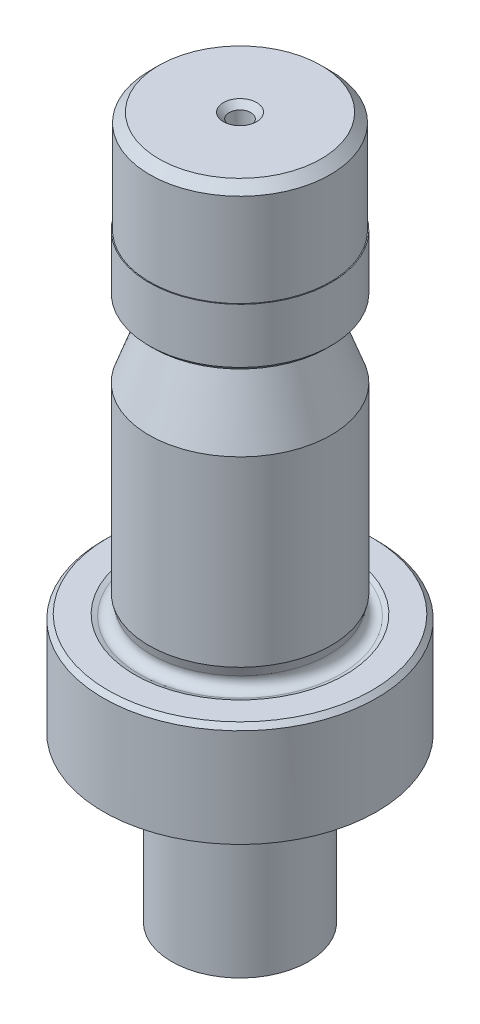
SolidWorks part; units mm, degrees
material "D2 (1.2379)"
ref_plane "Plano frontal" through (0, 0, 0) normal (0, 0, 1) x (1, 0, 0)
ref_plane "Plano superior" through (0, 0, 0) normal (0, 1, 0) x (1, 0, 0)
ref_plane "Plano direito" through (0, 0, 0) normal (1, 0, 0) x (0, 0, -1)
sketch "Esboço1" plane through (0, 0, 0) normal (0, 0, 1) x (1, 0, 0)
  line L0 (0, 77) -> (0, 0) construction
  line L1 (0, 77) -> (8.9, 77)
  line L2 (9.9, 76) -> (9.9, 65.8)
  line L3 (9.9, 65.8) -> (10, 65.8)
  line L4 (10, 65.8) -> (10, 59.8)
  line L5 (9.5, 59.3) -> (8.5164, 59.3)
  line L6 (7.5767, 57.958) -> (10, 51.3)
  line L7 (10, 51.3) -> (10, 31.3)
  line L8 (10, 31.3) -> (9.7321, 30.3)
  line L9 (11.0568, 29.1078) -> (11.5568, 29.3)
  line L10 (11.5568, 29.3) -> (14.5, 29.3)
  line L11 (15, 28.8) -> (15, 0)
  line L12 (15, 0) -> (0, 0)
  line L13 (8.9, 77) -> (9.9, 76)
  line L14 (14.5, 29.3) -> (15, 28.8)
  line L15 (10, 59.8) -> (9.5, 59.3)
  line L16 (0, 77) -> (0, 0)
  arc A0 (8.5164, 59.3) -> (7.5767, 57.958) centre (8.5164, 58.3) ccw
  arc A1 (9.7321, 30.3) -> (11.0568, 29.1078) centre (10.698, 30.0412) ccw
  point P3 (9.9, 77)
  point P6 (10, 59.3)
  point P15 (15, 29.3)
  dimension "D9" = 1
  dimension "D10" = 1
  dimension "D1" = 11.2
  dimension "D2" = 17.7
  dimension "D3" = 25.7
  dimension "D5" = 2
  dimension "D6" = 1
  dimension "D7" = 15
  dimension "D8" = 0.5
  dimension "D11" = 20
  dimension "D12" = 1
  dimension "D14" = 0.5
  dimension "D16" = 0.5
  dimension "D18" = 19.8
  dimension "D19" = 20
  dimension "D20" = 20
  dimension "Backing" = 30
  dimension "D22" = 77
  dimension "D4" = 30
revolve "Revolução1" add sketch "Esboço1" angle 360 about L0
hole_wizard "Furo de diâmetro 3/32 (0.09375)2" positions "Esboço8" profile "Esboço7" hole size "3/32" standard "Polegada Ansi"
sketch "Esboço8" plane through (0, 77, 0) normal (0, 1, 0) x (-1, 0, 0)
  point P4 (0, 0)
sketch "Esboço7" plane through (0, 77, 0) normal (1, 0, 0) x (0, 0, 1)
  line L0 (0, 0) -> (0, 3.7154)
  line L1 (0, 3.7154) -> (1.1906, 3)
  line L2 (1.1906, 3) -> (1.1906, 0.635)
  line L3 (1.1906, 0.635) -> (1.8256, 0)
  line L5 (1.8256, 0) -> (0, 0)
  line L6 (-1.1906, 0.635) -> (-1.8256, 0) construction
  line L10 (0, 3.7154) -> (-1.1906, 3) construction
  line L11 (0, -6.35) -> (0, 107.95) construction
  dimension "Hole Dia." = 2.3812
  dimension "Hole Depth" = 3
  dimension "Near C'Sink Dia." = 3.6512
  dimension "Near C'Sink Angle" = 90
  dimension "Drill Angle" = 118
sketch "Esboço10" plane through (0, 0, 0) normal (0, -1, 0) x (1, 0, 0)
  circle A0 centre (0, 0) radius 7.5
  dimension "Hole_Diameter" = 15
extrude "Corte-extrusão2" cut sketch "Esboço10" against normal blind 18 flip side to cut
fillet "Filete1" radius 3 1 edges at (7.5, 18, 0)
equation "\"hole_diameter\" = 15.0"
equation "\"die_clearance\" = 0.6000000000000001"
equation "\"punch_base\" = 30"
equation "\"die_base\" = 60"
equation "\"cutting_force\" = 1440.0"
equation "\"Hole_Diameter@Esboço10\"=\"hole_diameter\""
equation "\"Backing@Esboço1\"=\"punch_base\""
